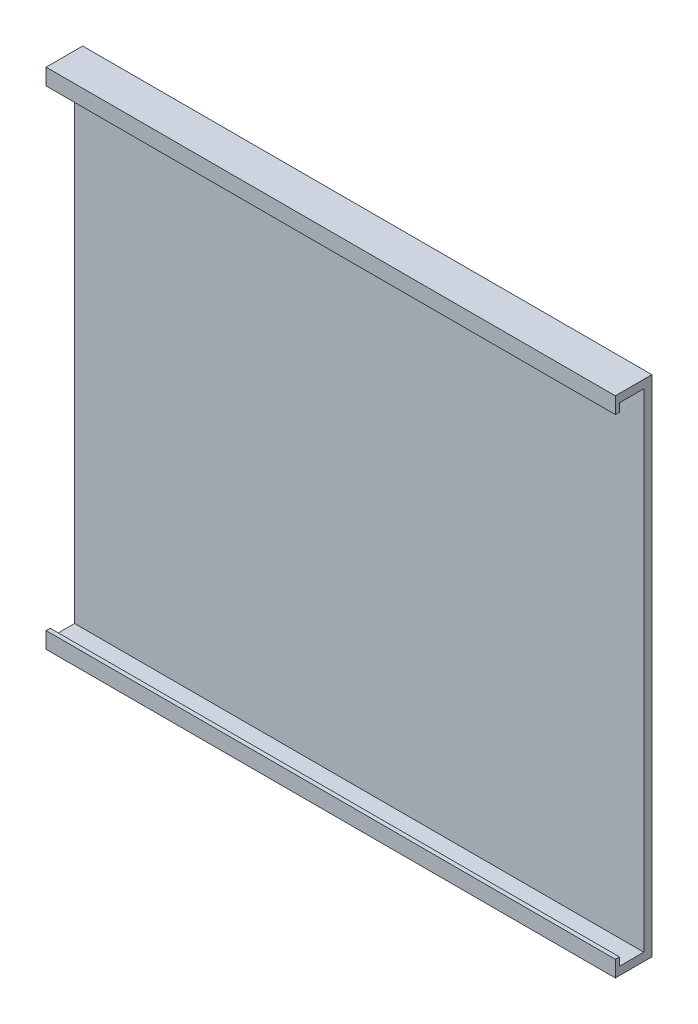
SolidWorks part; units mm, degrees
ref_plane "前视基准面" through (0, 0, 0) normal (0, 0, 1) x (1, 0, 0)
ref_plane "上视基准面" through (0, 0, 0) normal (0, 1, 0) x (1, 0, 0)
ref_plane "右视基准面" through (0, 0, 0) normal (1, 0, 0) x (0, 0, -1)
other "Configuration Table"
sketch "草图1" plane through (0, 0, 0) normal (0, 0, 1) x (1, 0, 0)
  line L1 (-45.8, 45.6) -> (24.2, 45.6)
  line L2 (-45.8, 45.6) -> (-45.8, -16.4)
  line L3 (-45.8, -16.4) -> (24.2, -16.4)
  line L4 (24.2, 45.6) -> (24.2, -16.4)
  dimension "D1" = 70
  dimension "D2" = 62
extrude "凸台-拉伸1" add sketch "草图1" along normal blind 1 contours L2 L1 L4 L3
sketch "草图2" plane through (0, 0, 1) normal (0, 0, 1) x (1, 0, 0)
  line L0 (24.2, 45.6) -> (24.2, -16.4) construction
  line L1 (-45.8, 45.6) -> (24.2, 45.6)
  line L2 (-45.8, 45.6) -> (-45.8, 43.6)
  line L3 (-45.8, 43.6) -> (24.2, 43.6)
  line L4 (24.2, 45.6) -> (24.2, 43.6)
  line L5 (-45.8, 45.6) -> (-45.8, -16.4) construction
  line L6 (-45.8, -14.4) -> (24.2, -14.4)
  line L7 (-45.8, -14.4) -> (-45.8, -16.4)
  line L8 (-45.8, -16.4) -> (24.2, -16.4)
  line L9 (24.2, -14.4) -> (24.2, -16.4)
  line L10 (-45.8, -16.4) -> (24.2, -16.4) construction
  dimension "D1" = 2
  dimension "D2" = 2
extrude "凸台-拉伸2" add sketch "草图2" along normal blind 3.5
sketch "草图6" plane through (-45.8, 0, 0) normal (-1, 0, 0) x (0, 0, 1)
  line L0 (4.5, 43.6) -> (1, 43.6) construction
  line L1 (1, 43.6) -> (4, 43.6)
  line L2 (1, 43.6) -> (1, 44.6)
  line L3 (1, 44.6) -> (4, 44.6)
  line L4 (4, 43.6) -> (4, 44.6)
  line L6 (1, -14.4) -> (4, -14.4)
  line L7 (1, -14.4) -> (1, -15.4)
  line L8 (1, -15.4) -> (4, -15.4)
  line L9 (4, -14.4) -> (4, -15.4)
  line L11 (4.5, 45.6) -> (4.5, 43.6) construction
  line L12 (4.5, 45.6) -> (0, 45.6) construction
  line L13 (4.5, -14.4) -> (4.5, -16.4) construction
  line L14 (4.5, -16.4) -> (0, -16.4) construction
  dimension "D1" = 0.5
  dimension "D2" = 1
  dimension "D3" = 0.5
  dimension "D4" = 1
extrude "切除-拉伸1" cut sketch "草图6" against normal through all
